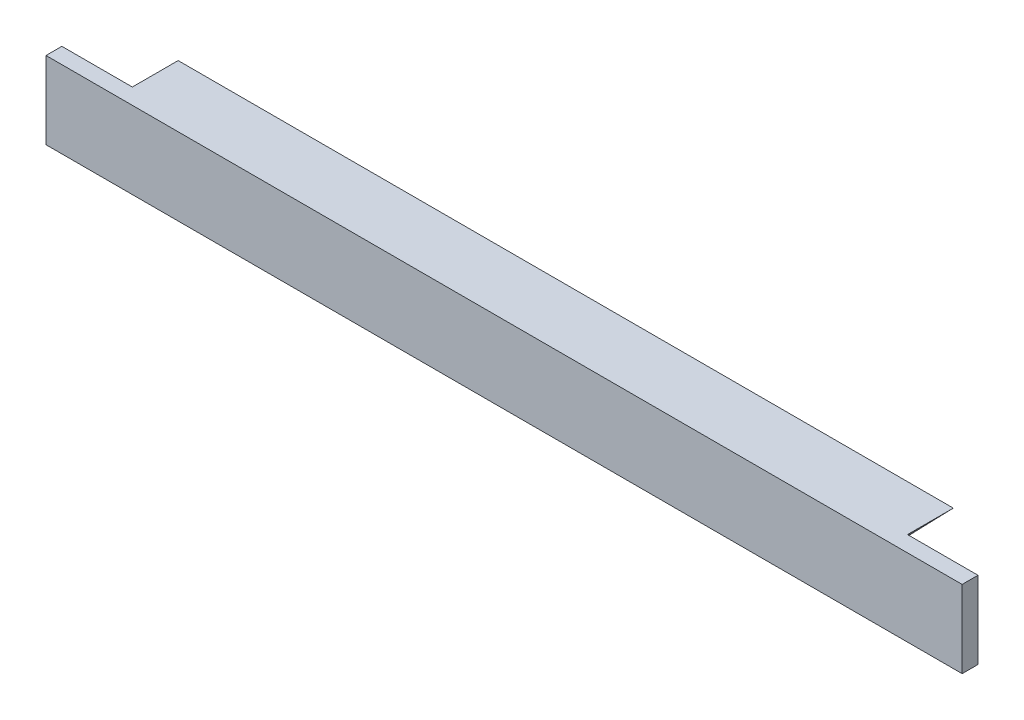
SolidWorks part; units mm, degrees
ref_plane "Ön Düzlem" through (0, 0, 0) normal (0, 0, 1) x (1, 0, 0)
ref_plane "Üst Düzlem" through (0, 0, 0) normal (0, 1, 0) x (1, 0, 0)
ref_plane "Sağ Düzlem" through (0, 0, 0) normal (1, 0, 0) x (0, 0, -1)
sketch "Çizim1" plane through (0, 0, 0) normal (0, 0, 1) x (1, 0, 0)
  line L0 (0, 4.3882) -> (0, -1.988) construction
  line L1 (22, 4.3882) -> (18.6341, 0.9129)
  line L2 (-22, 4.3882) -> (-18.6341, 0.9129)
  line L3 (-22, 4.3882) -> (22, 4.3882)
  line L4 (16.4791, 0) -> (-16.4791, 0)
  line L5 (0, 0) -> (37.6602, 0) construction
  arc A0 (-18.6341, 0.9129) -> (-16.4791, 0) centre (-16.4791, 3) ccw
  arc A1 (18.6341, 0.9129) -> (16.4791, 0) centre (16.4791, 3) cw
  point P6 (0, 0)
  point P8 (0, 4.3882)
  dimension "D2" = 3
  dimension "D1" = 22
  dimension "D3" = 44
  dimension "D4" = 4.3882
extrude "Yükseklik-Ekstrüzyon1" add sketch "Çizim1" along normal blind 2.6
sketch "Çizim2" plane through (0, 0, 2.6) normal (0, 0, 1) x (1, 0, 0)
  line L0 (0, 0) -> (0, 17.683) construction
  line L1 (22, 4.3882) -> (-22, 4.3882) construction
  line L2 (26, 4.3882) -> (-26, 4.3882)
  line L3 (26, 4.3882) -> (26, 0)
  line L4 (26, 0) -> (-26, 0)
  line L5 (-26, 4.3882) -> (-26, 0)
  line L6 (-16.4791, 0) -> (16.4791, 0) construction
  dimension "D1" = 52
  dimension "D2" = 26
extrude "Yükseklik-Ekstrüzyon3" add sketch "Çizim2" along normal blind 0.9
